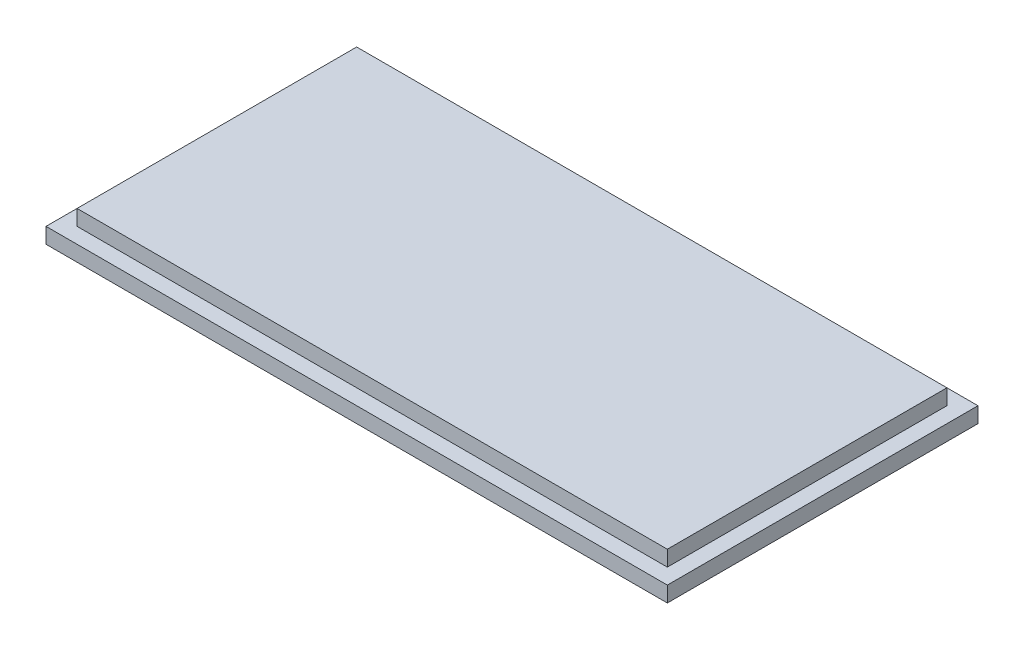
SolidWorks part; units mm, degrees
ref_plane "Front Plane" through (0, 0, 0) normal (0, 0, 1) x (1, 0, 0)
ref_plane "Top Plane" through (0, 0, 0) normal (0, 1, 0) x (1, 0, 0)
ref_plane "Right Plane" through (0, 0, 0) normal (1, 0, 0) x (0, 0, -1)
sketch "Sketch1" plane through (0, 0, 0) normal (0, 1, 0) x (1, 0, 0)
  line L1 (0, 0) -> (200, 0)
  line L2 (0, 0) -> (0, 100)
  line L3 (0, 100) -> (200, 100)
  line L4 (200, 0) -> (200, 100)
  dimension "D1" = 100
  dimension "D2" = 200
extrude "Boss-Extrude1" add sketch "Sketch1" along normal blind 5
sketch "Sketch2" plane through (0, 5, 0) normal (0, 1, 0) x (1, 0, 0)
  line L0 (0, 50) -> (200, 50) construction
  line L1 (0, 100) -> (0, 0) construction
  line L2 (200, 0) -> (200, 100) construction
  line L3 (100, 50) -> (100, 100) construction
  line L4 (200, 100) -> (0, 100) construction
  line L6 (5, 95) -> (195, 95)
  line L7 (5, 95) -> (5, 5)
  line L8 (5, 5) -> (195, 5)
  line L9 (195, 95) -> (195, 5)
  line L10 (5, 95) -> (195, 5) construction
  line L11 (5, 5) -> (195, 95) construction
  dimension "D1" = 5
  dimension "D2" = 5
extrude "Boss-Extrude2" add sketch "Sketch2" along normal blind 5
